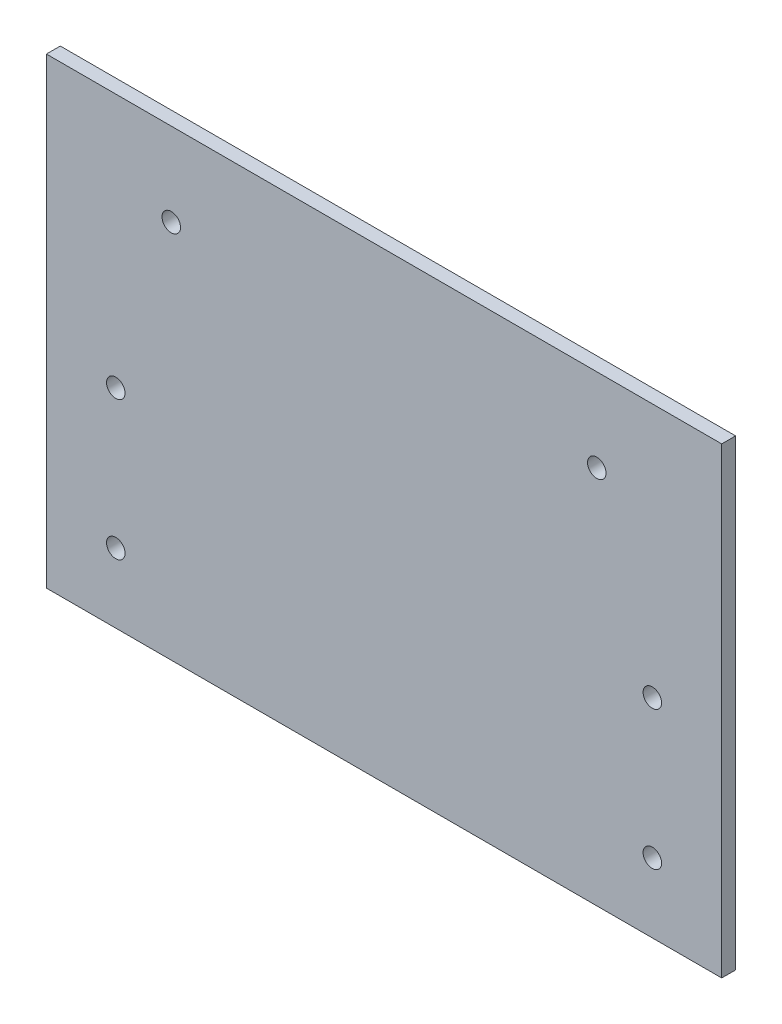
SolidWorks part; units mm, degrees
ref_plane "Front Plane" through (0, 0, 0) normal (0, 0, 1) x (1, 0, 0)
ref_plane "Top Plane" through (0, 0, 0) normal (0, 1, 0) x (1, 0, 0)
ref_plane "Right Plane" through (0, 0, 0) normal (1, 0, 0) x (0, 0, -1)
sketch "Sketch1" plane through (0, 0, 0) normal (0, 0, 1) x (1, 0, 0)
  line L1 (-74.1235, 86.0212) -> (71.8765, 86.0212)
  line L2 (-74.1235, 86.0212) -> (-74.1235, -13.9788)
  line L3 (-74.1235, -13.9788) -> (71.8765, -13.9788)
  line L4 (71.8765, 86.0212) -> (71.8765, -13.9788)
  dimension "D1" = 146
  dimension "D2" = 100
extrude "Boss-Extrude1" add sketch "Sketch1" along normal blind 3
sketch "Sketch2" plane through (0, 0, 0) normal (0, 0, -1) x (-1, 0, 0)
  circle A0 centre (59.1235, 1.0212) radius 2
  circle A1 centre (-56.8765, 1.0212) radius 2
  dimension "D1" = 4
  dimension "D2" = 4
extrude "Cut-Extrude1" cut sketch "Sketch2" against normal through all
sketch "Sketch3" plane through (0, 0, 0) normal (0, 0, -1) x (-1, 0, 0)
  circle A0 centre (-56.8765, 31.0212) radius 2
  circle A1 centre (59.1235, 31.0212) radius 2
  dimension "D1" = 4
extrude "Cut-Extrude2" cut sketch "Sketch3" against normal through all
sketch "Sketch4" plane through (0, 0, 0) normal (0, 0, -1) x (-1, 0, 0)
  circle A0 centre (-44.8668, 68.0399) radius 2
  circle A1 centre (47.1242, 68.0399) radius 2
  point P4 (0, 0)
  dimension "D1" = 4
  dimension "D2" = 4
extrude "Cut-Extrude3" cut sketch "Sketch4" against normal through all
